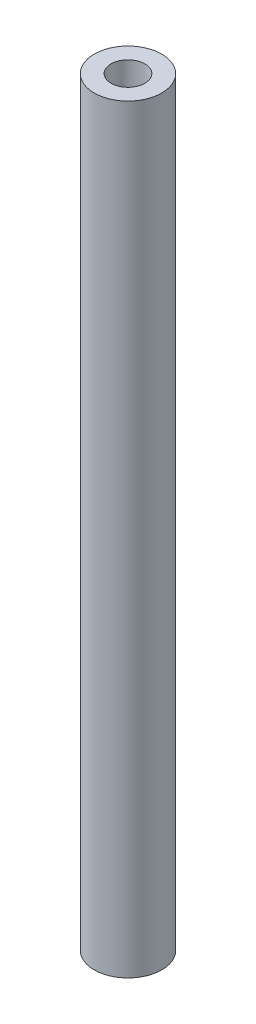
SolidWorks part; units mm, degrees
material "3.0205 (EN-AW 1200)"
ref_plane "Front" through (0, 0, 0) normal (0, 0, 1) x (1, 0, 0)
ref_plane "Top" through (0, 0, 0) normal (0, 1, 0) x (1, 0, 0)
ref_plane "Right" through (0, 0, 0) normal (1, 0, 0) x (0, 0, -1)
sketch "草图1" plane through (0, 0, 0) normal (0, 1, 0) x (1, 0, 0)
  circle A0 centre (0, 0) radius 4
  circle A1 centre (0, 0) radius 2
extrude "凸台-拉伸1" add sketch "草图1" along normal blind 90
